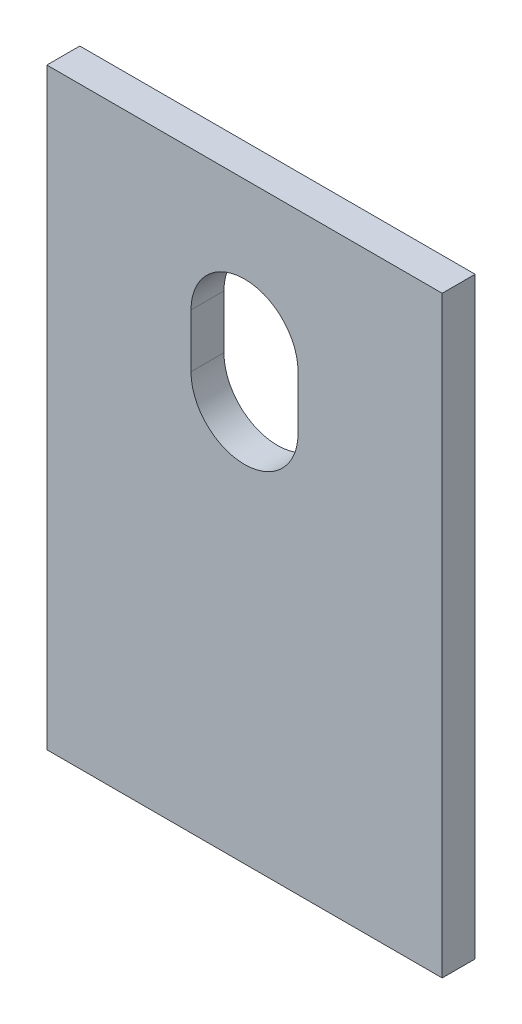
SolidWorks part; units mm, degrees
ref_plane "Front Plane" through (0, 0, 0) normal (0, 0, 1) x (1, 0, 0)
ref_plane "Top Plane" through (0, 0, 0) normal (0, 1, 0) x (1, 0, 0)
ref_plane "Right Plane" through (0, 0, 0) normal (1, 0, 0) x (0, 0, -1)
sketch "Sketch1" plane through (0, 0, 0) normal (0, 1, 0) x (1, 0, 0)
  line L1 (0, 0) -> (76.2, 0)
  line L2 (0, 0) -> (0, 6.35)
  line L3 (0, 6.35) -> (76.2, 6.35)
  line L4 (76.2, 0) -> (76.2, 6.35)
  dimension "D1" = 76.2
  dimension "D2" = 6.35
extrude "Boss-Extrude1" add sketch "Sketch1" along normal blind 114.3
sketch "Sketch2" plane through (0, 0, 0) normal (0, 0, 1) x (1, 0, 0)
  line L0 (38.1, 114.3) -> (38.1, -19.4121) construction
  line L1 (0, 114.3) -> (76.2, 114.3) construction
  line L2 (76.2, 114.3) -> (76.2, 0) construction
  line L3 (38.1, 87.3125) -> (64.9441, 87.3125) construction
  line L5 (38.1, 26.9875) -> (82.1922, 26.9875) construction
  line L6 (0, 0) -> (76.2, 0) construction
  line L8 (38.1, 87.3125) -> (38.1, 76.9938) construction
  line L9 (48.4188, 87.3125) -> (48.4188, 76.9938)
  line L10 (27.7813, 87.3125) -> (27.7813, 76.9938)
  arc A2 (48.4188, 87.3125) -> (27.7813, 87.3125) centre (38.1, 87.3125) ccw
  arc A3 (27.7813, 76.9938) -> (48.4188, 76.9938) centre (38.1, 76.9938) ccw
  point P19 (38.1, 82.1531)
  dimension "D2" = 20.6375
  dimension "D1" = 38.1
  dimension "D3" = 26.9875
extrude "Cut-Extrude1" cut sketch "Sketch2" against normal through all
